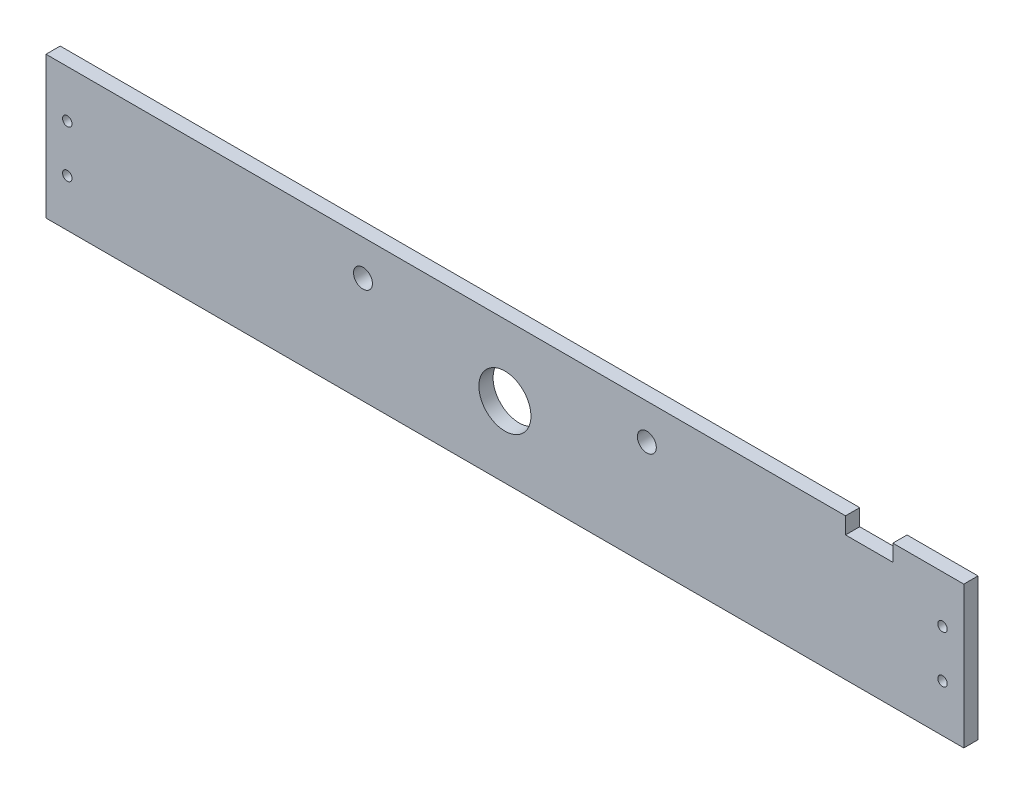
SolidWorks part; units mm, degrees
material "Acrylic (Medium-high impact)"
ref_plane "Front Plane" through (0, 0, 0) normal (0, 0, 1) x (1, 0, 0)
ref_plane "Top Plane" through (0, 0, 0) normal (0, 1, 0) x (1, 0, 0)
ref_plane "Right Plane" through (0, 0, 0) normal (1, 0, 0) x (0, 0, -1)
sketch "Sketch1" plane through (0, 0, 0) normal (0, 0, 1) x (1, 0, 0)
  line L0 (0, -1000) -> (0, 49000) construction
  line L1 (-194, -30) -> (194, -30)
  line L3 (-194, 30) -> (194, 30)
  line L7 (-1000, 0) -> (49000, 0) construction
  line L8 (194, 30) -> (194, -30)
  line L20 (-194, 30) -> (-194, -30)
  line L25 (-1000, 15) -> (49000, 15) construction
  line L26 (164, 30) -> (144, 30)
  line L27 (164, 30) -> (164, 23)
  line L28 (164, 23) -> (144, 23)
  line L29 (144, 30) -> (144, 23)
  circle A4 centre (60, 15) radius 4
  circle A5 centre (-60, 15) radius 4
  circle A14 centre (0, 0) radius 11
  circle A15 centre (185, 10) radius 2
  circle A16 centre (185, -10) radius 2
  circle A17 centre (-185, -10) radius 2
  circle A18 centre (-185, 10) radius 2
  point P0 (0, 0)
  point P19 (188.882, 9.2738)
  point P24 (0, -30)
  dimension "D7" = 20
  dimension "D8" = 30
  dimension "D9" = 4
  dimension "D10" = 60
  dimension "D11" = 9
  dimension "D4" = 8
  dimension "D13" = 388
  dimension "D14" = 60
  dimension "D2" = 22
  dimension "D5" = 60
  dimension "D12" = 20
  dimension "D3" = 15
  dimension "D6" = 7
  dimension "D16" = 15
extrude "Boss-Extrude1" add sketch "Sketch1" along normal blind 6
